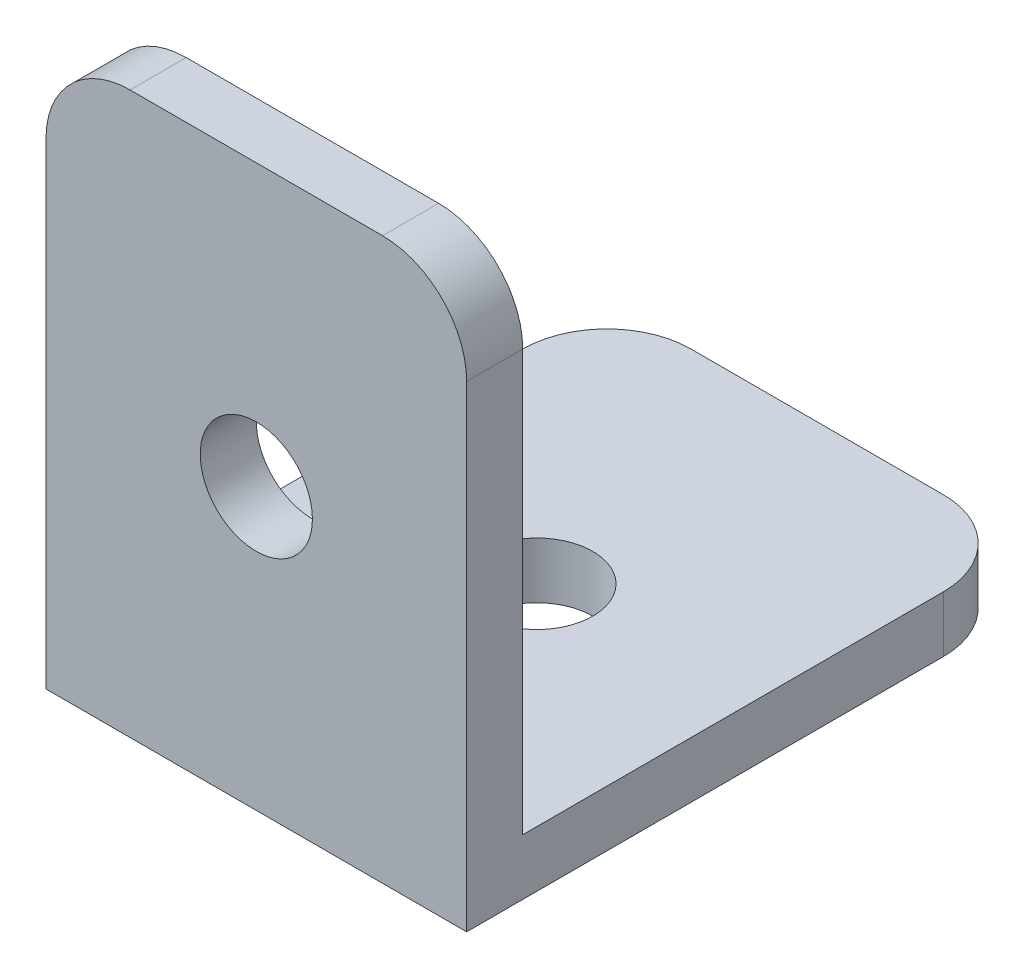
SolidWorks part; units mm, degrees
ref_plane "Front Plane" through (0, 0, 0) normal (0, 0, 1) x (1, 0, 0)
ref_plane "Top Plane" through (0, 0, 0) normal (0, 1, 0) x (1, 0, 0)
ref_plane "Right Plane" through (0, 0, 0) normal (1, 0, 0) x (0, 0, -1)
sketch "Sketch1" plane through (0, 0, 0) normal (0, 1, 0) x (1, 0, 0)
  line L0 (0, 0) -> (0, 15)
  line L1 (3, 18) -> (12, 18)
  line L2 (15, 15) -> (15, 0)
  line L3 (15, 0) -> (0, 0)
  arc A0 (12, 18) -> (15, 15) centre (12, 15) cw
  arc A1 (0, 15) -> (3, 18) centre (3, 15) cw
  circle A2 centre (7.5, 8) radius 2
  point P9 (0, 18)
  dimension "D3" = 3
  dimension "D4" = 4
  dimension "D1" = 15
  dimension "D2" = 18
  dimension "D5" = 10
  dimension "D6" = 7.5
extrude "Boss-Extrude1" add sketch "Sketch1" along normal blind 2
sketch "Sketch2" plane through (0, 0, 0) normal (0, 0, 1) x (1, 0, 0)
  line L0 (0, 0) -> (0, 17)
  line L1 (15, 0) -> (15, 17)
  line L2 (12, 20) -> (3, 20)
  line L3 (0, 0) -> (15, 0) construction
  arc A0 (15, 17) -> (12, 20) centre (12, 17) ccw
  arc A1 (0, 17) -> (3, 20) centre (3, 17) cw
  circle A2 centre (7.5, 10) radius 2
  line M3 (0, 0) -> (15, 0)
  line M4 (15, 0) -> (15, 2)
  line M5 (15, 2) -> (0, 2)
  line M6 (0, 2) -> (0, 0)
  dimension "D1" = 3
  dimension "D2" = 4
  dimension "D3" = 10
  dimension "D4" = 7.5
  dimension "D5" = 20
extrude "Boss-Extrude2" add sketch "Sketch2" along normal blind 2 contours A1 L0 L1 A0 L2 A2 M5 | M6 M3 M4 M5
